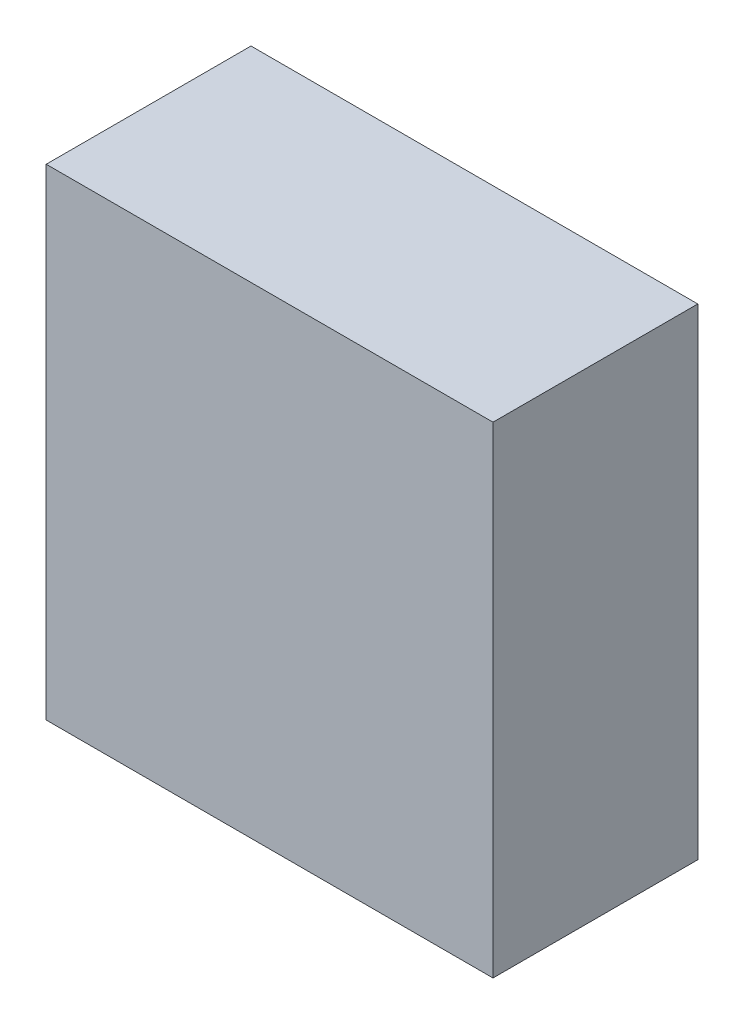
SolidWorks part; units mm, degrees
ref_plane "Front Plane" through (0, 0, 0) normal (0, 0, 1) x (1, 0, 0)
ref_plane "Top Plane" through (0, 0, 0) normal (0, 1, 0) x (1, 0, 0)
ref_plane "Right Plane" through (0, 0, 0) normal (1, 0, 0) x (0, 0, -1)
sketch "Sketch1" plane through (0, 0, 0) normal (0, 0, 1) x (1, 0, 0)
  line L1 (0, 0) -> (168, 0)
  line L2 (0, 0) -> (0, -181)
  line L3 (0, -181) -> (168, -181)
  line L4 (168, 0) -> (168, -181)
  dimension "D1" = 181
  dimension "D2" = 168
extrude "Boss-Extrude1" add sketch "Sketch1" along normal blind 77
